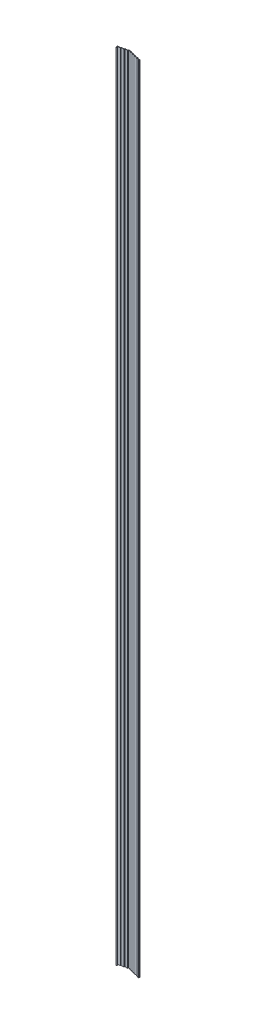
SolidWorks part; units mm, degrees
material "6463-T6"
ref_plane "Front Plane" through (0, 0, 0) normal (0, 0, 1) x (1, 0, 0)
ref_plane "Top Plane" through (0, 0, 0) normal (0, 1, 0) x (1, 0, 0)
ref_plane "Right Plane" through (0, 0, 0) normal (1, 0, 0) x (0, 0, -1)
sketch "Sketch1" plane through (0, 0, 0) normal (0, 1, 0) x (1, 0, 0)
  line L0 (50.7924, 25.4) -> (50.7924, 0) construction
  line L1 (0, 0) -> (101.5848, 0) construction
  line L2 (0, 0) -> (0, 25.4) construction
  line L3 (0, 25.4) -> (101.5848, 25.4) construction
  line L4 (101.5848, 0) -> (101.5848, 25.4) construction
  line L5 (0, 12.7) -> (50.7924, 12.7) construction
  line L6 (50.7924, 12.7) -> (101.5848, 12.7) construction
  line L7 (25.3962, 12.7) -> (25.3962, 25.4) construction
  line L8 (76.1886, 12.7) -> (76.1886, 25.4) construction
  line L9 (25.3962, 12.7) -> (25.3962, 0) construction
  line L10 (76.1886, 12.7) -> (76.1886, 0) construction
  line L11 (25.3962, 19.05) -> (0, 19.05) construction
  line L12 (25.3962, 19.05) -> (50.7924, 19.05) construction
  line L13 (50.7924, 19.05) -> (76.1886, 19.05) construction
  line L14 (76.1886, 19.05) -> (101.5848, 19.05) construction
  line L15 (25.3962, 6.35) -> (0, 6.35) construction
  line L16 (25.3962, 6.35) -> (50.7924, 6.35) construction
  line L17 (50.7924, 6.35) -> (76.1886, 6.35) construction
  line L18 (76.1886, 6.35) -> (101.5848, 6.35) construction
  line L19 (12.6981, 19.05) -> (12.6981, 25.4) construction
  line L20 (12.6981, 19.05) -> (12.6981, 0) construction
  line L21 (38.0943, 19.05) -> (38.0943, 25.4) construction
  line L22 (38.0943, 19.05) -> (38.0943, 0) construction
  line L23 (63.4905, 19.05) -> (63.4905, 25.4) construction
  line L24 (63.4905, 19.05) -> (63.4905, 0) construction
  line L25 (88.8867, 19.05) -> (88.8867, 25.4) construction
  line L26 (88.8867, 19.05) -> (88.8867, 0) construction
  line L27 (0, 6.35) -> (0, 12.7)
  line L28 (0, 12.7) -> (12.6981, 12.7)
  line L29 (12.6981, 12.7) -> (12.6981, 15.875)
  line L30 (12.6981, 15.875) -> (25.3962, 15.875)
  line L31 (25.3962, 15.875) -> (25.3962, 19.05)
  line L32 (25.3962, 19.05) -> (38.0943, 19.05)
  line L33 (38.0943, 19.05) -> (38.0943, 15.875)
  line L34 (38.0943, 15.875) -> (50.7924, 15.875)
  line L35 (50.7924, 15.875) -> (50.7924, 12.7)
  line L36 (50.7924, 12.7) -> (63.4905, 12.7)
  line L37 (63.4905, 12.7) -> (63.4905, 9.525)
  line L38 (63.4905, 9.525) -> (76.1886, 9.525)
  line L39 (76.1886, 9.525) -> (76.1886, 6.35)
  line L40 (76.1886, 6.35) -> (88.8867, 6.35)
  line L41 (88.8867, 6.35) -> (88.8867, 9.525)
  line L42 (88.8867, 9.525) -> (101.5848, 9.525)
  line L43 (101.5848, 9.525) -> (101.5848, 6.35)
  line L45 (1.524, 6.35) -> (1.524, 11.176)
  line L46 (1.524, 11.176) -> (14.2221, 11.176)
  line L47 (14.2221, 11.176) -> (14.2221, 14.351)
  line L48 (14.2221, 14.351) -> (26.9202, 14.351)
  line L49 (26.9202, 14.351) -> (26.9202, 17.526)
  line L50 (26.9202, 17.526) -> (36.5703, 17.526)
  line L51 (36.5703, 17.526) -> (36.5703, 14.351)
  line L52 (36.5703, 14.351) -> (49.2684, 14.351)
  line L53 (49.2684, 14.351) -> (49.2684, 11.176)
  line L54 (49.2684, 11.176) -> (61.9665, 11.176)
  line L55 (61.9665, 11.176) -> (61.9665, 8.001)
  line L56 (61.9665, 8.001) -> (74.6646, 8.001)
  line L57 (74.6646, 8.001) -> (74.6646, 4.826)
  line L58 (74.6646, 4.826) -> (90.4107, 4.826)
  line L59 (90.4107, 4.826) -> (90.4107, 8.001)
  line L60 (90.4107, 8.001) -> (100.0608, 8.001)
  line L61 (100.0608, 8.001) -> (100.0608, 6.35)
  line L62 (0, 6.35) -> (-1.524, 6.35)
  line L63 (-1.524, 6.35) -> (-1.524, 4.826)
  line L64 (-1.524, 4.826) -> (1.524, 4.826)
  line L65 (1.524, 4.826) -> (1.524, 6.35)
  line L66 (88.8867, 9.525) -> (0, 9.525) construction
  line L67 (88.8867, 6.35) -> (88.8867, 4.826)
  line L68 (0, 9.525) -> (-12.7, 9.525)
  line L69 (0, 8.001) -> (1.524, 8.001)
  line L70 (-12.7, 9.525) -> (-12.7, 4.826)
  line L71 (-12.7, 4.826) -> (-11.176, 4.826)
  line L72 (-11.176, 4.826) -> (-11.176, 8.001)
  line L73 (-11.176, 8.001) -> (0, 8.001)
  line L74 (74.6646, 4.826) -> (-11.176, 4.826) construction
  dimension "D1" = 101.5848
  dimension "D2" = 25.4
  dimension "D3" = 3.175
  dimension "D4" = 3.175
  dimension "D6" = 1.524
  dimension "D7" = 1.524
  dimension "D8" = 1.524
  dimension "D9" = 1.524
  dimension "D10" = 12.7
  dimension "D5" = 1.524
extrude "Boss-Extrude1" add sketch "Sketch1" along normal blind 3505.2 contours L27 L69 L45 L46 L47 L48 L49 L50 L51 L52 L53 L54 L55 L56 L57 L58 L67 L40 L39 L38 L37 L36 L35 L34 L33 L32 L31 L30 L29 L28 | L72 L73 L27 L68 L70 L71
sketch "Sketch2" plane through (0, 3505.2, 0) normal (0, 1, 0) x (1, 0, 0)
  line L0 (-12.7, 5.588) -> (88.8867, 5.588) construction
  line L1 (-12.7, 9.525) -> (-12.7, 4.826) construction
  line L2 (88.8867, 6.35) -> (88.8867, 4.826) construction
  line L3 (76.1886, 6.35) -> (88.8867, 6.35) construction
  line L4 (88.8867, 5.588) -> (88.6093, 4.826)
  line L5 (74.6646, 4.826) -> (88.8867, 4.826) construction
  line L6 (88.6093, 4.826) -> (88.8867, 4.826)
  line L7 (88.8867, 4.826) -> (88.8867, 5.588)
  line L8 (-12.7, 5.588) -> (-12.4227, 4.826)
  line L9 (-12.7, 4.826) -> (-11.176, 4.826) construction
  line L10 (-12.4227, 4.826) -> (-12.7, 4.826)
  line L11 (-12.7, 4.826) -> (-12.7, 5.588)
  dimension "D1" = 0.762
  dimension "D2" = 20
  dimension "D3" = 20
extrude "Cut-Extrude1" cut sketch "Sketch2" against normal through all
sketch "Sketch3" plane through (0, 3505.2, 0) normal (0, 1, 0) x (1, 0, 0)
  line L0 (-12.4227, 4.826) -> (-12.3533, 4.6355)
  line L1 (-12.4227, 4.826) -> (-12.7, 5.588) construction
  line L2 (87.4585, 1.7112) -> (87.232, 1.089)
  line L4 (-12.7, 9.525) -> (-12.7, 5.588) construction
  line L5 (-9.906, 4.6355) -> (-12.3533, 4.6355)
  line L6 (-9.906, 6.1595) -> (-10.414, 6.1595)
  line L8 (-9.906, 2.2225) -> (-10.9309, 2.2225)
  line L9 (-11.289, 1.7112) -> (-11.0625, 1.089)
  line L10 (88.8867, 6.35) -> (-12.7, 6.35) construction
  line L11 (38.0848, 21.7417) -> (38.0848, -8.6113) construction
  line L12 (86.0755, 2.2225) -> (87.1005, 2.2225)
  line L13 (74.6646, 4.826) -> (88.6093, 4.826) construction
  line L14 (86.0755, 4.6355) -> (88.5228, 4.6355)
  line L15 (88.6093, 4.826) -> (88.5228, 4.6355)
  line L17 (82.3484, 4.826) -> (88.6093, 4.826)
  line L18 (-12.4227, 4.826) -> (-11.176, 4.826) construction
  line L19 (-11.176, 4.826) -> (-11.176, 8.001) construction
  line L20 (-12.4227, 4.826) -> (-11.176, 4.826)
  line L21 (-11.176, 4.826) -> (-11.176, 6.9215)
  arc A0 (-9.906, 2.2225) -> (-9.906, 4.6355) centre (-9.906, 3.429) ccw
  arc A1 (-10.834, 0.861) -> (-9.906, 6.1595) centre (-9.906, 3.429) ccw
  arc A2 (87.0035, 0.861) -> (83.3592, 3.7067) centre (86.0755, 3.429) cw
  arc A3 (86.0755, 2.2225) -> (86.0755, 4.6355) centre (86.0755, 3.429) cw
  arc A4 (82.3484, 4.826) -> (83.3592, 3.7067) centre (82.3484, 3.81) cw
  arc A5 (87.0035, 0.861) -> (87.232, 1.089) centre (86.874, 1.2193) ccw
  arc A6 (87.4585, 1.7112) -> (87.1005, 2.2225) centre (87.1005, 1.8415) ccw
  arc A7 (-10.834, 0.861) -> (-11.0625, 1.089) centre (-10.7045, 1.2193) cw
  arc A8 (-10.9309, 2.2225) -> (-11.289, 1.7112) centre (-10.9309, 1.8415) ccw
  arc A9 (-11.176, 6.9215) -> (-10.414, 6.1595) centre (-10.414, 6.9215) ccw
  point P36 (87.1738, 0.9291)
  point P39 (87.6446, 2.2225)
  point P42 (-11.0043, 0.9291)
  point P45 (-11.4751, 2.2225)
  dimension "D1" = 2.413
  dimension "D2" = 5.461
  dimension "D6" = 1.016
  dimension "D7" = 0.381
  dimension "D8" = 0.381
  dimension "D9" = 0.762
  dimension "D3" = 2.921
  dimension "D4" = 2.794
  dimension "D5" = 50.7848
extrude "Boss-Extrude2" add sketch "Sketch3" against normal through all
fillet "Fillet1" radius 0.508 2 edges at (88.5228, 1752.6, -4.6355) (-12.3533, 1752.6, -4.6355)
